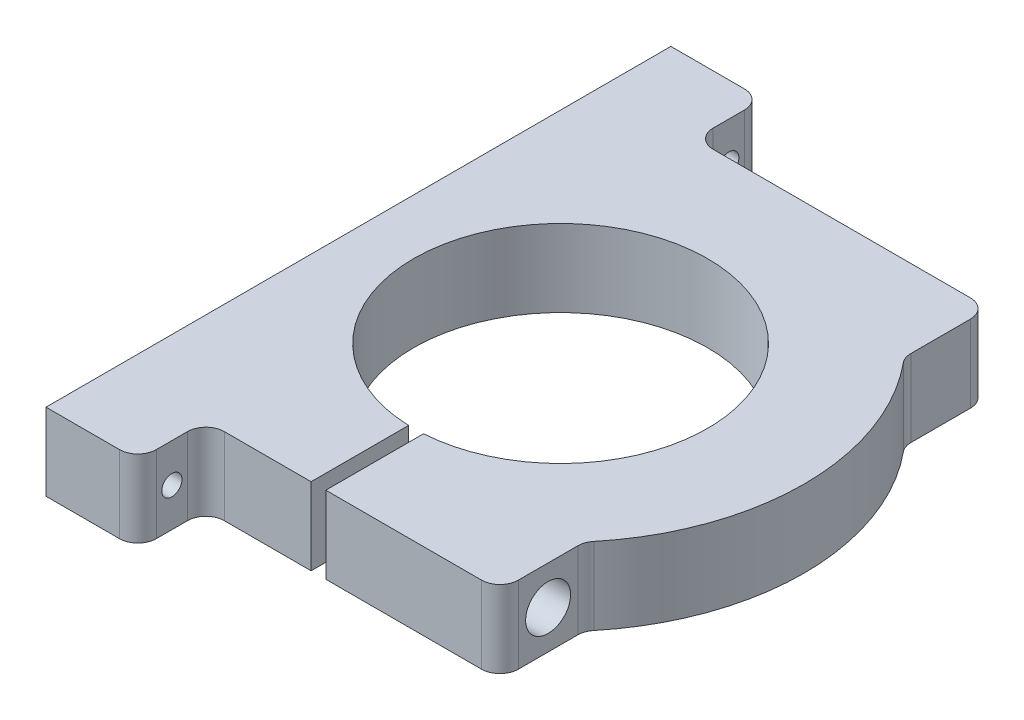
SolidWorks part; units mm, degrees
ref_plane "Piano frontale" through (0, 0, 0) normal (0, 0, 1) x (1, 0, 0)
ref_plane "Piano superiore" through (0, 0, 0) normal (0, 1, 0) x (1, 0, 0)
ref_plane "Piano destro" through (0, 0, 0) normal (1, 0, 0) x (0, 0, -1)
sketch "Sketch1" plane through (0, 0, -219.72) normal (0, -1, 0) x (1, 0, 0)
  line L2 (7.3254, -97.2179) -> (7.3254, -57.6696) construction
  line L3 (-32.6746, -97.2179) -> (7.3254, -97.2179) construction
  line L4 (17.3254, -30.7179) -> (-30.0496, -30.7179)
  line L5 (-62.6746, -30.7179) -> (-62.6746, -12.2179)
  line L6 (-62.6746, -12.2179) -> (-87.6746, -12.2179)
  line L7 (-34.0496, -30.7179) -> (-62.6746, -30.7179)
  line L8 (-40.0496, -30.7179) -> (-40.0496, -68.1385) construction
  line L9 (-24.0496, -68.4844) -> (-24.0496, -30.7179) construction
  line L10 (-87.6746, -182.2179) -> (-62.6746, -182.2179)
  line L11 (-62.6746, -182.2179) -> (-62.6746, -163.7179)
  line L12 (-87.6746, -22.2179) -> (-87.6746, -172.2179) construction
  line L13 (-62.6746, -163.7179) -> (17.3254, -163.7179)
  line L14 (17.3254, -163.7179) -> (17.3254, -140.6812)
  line L15 (17.3254, -53.7545) -> (17.3254, -30.7179)
  line L16 (-72.6746, -153.7179) -> (7.3254, -153.7179) construction
  line L17 (-34.0496, -40.7179) -> (-72.6746, -40.7179) construction
  line L18 (-34.0496, -57.2415) -> (-34.0496, -40.7179) construction
  line L19 (-30.0496, -40.7179) -> (-30.0496, -57.3041) construction
  line L21 (17.3254, -30.7179) -> (-40.0496, -30.7179) construction
  line L23 (-24.0496, -30.7179) -> (-62.6746, -30.7179) construction
  line L24 (-30.0496, -30.7179) -> (-30.0496, -57.3041)
  line L25 (-34.0496, -57.2415) -> (-34.0496, -30.7179)
  line L29 (-87.6746, -12.2179) -> (-87.6746, -182.2179)
  line L36 (-62.6746, -12.2179) -> (-97.6746, -12.2179) construction
  line L37 (-97.6746, -12.2179) -> (-97.6746, -182.2179) construction
  line L38 (-97.6746, -182.2179) -> (-62.6746, -182.2179) construction
  line L39 (-62.6746, -182.2179) -> (-62.6746, -163.7179) construction
  line L40 (-62.6746, -30.7179) -> (-62.6746, -12.2179) construction
  line L41 (-72.6746, -172.2179) -> (-72.6746, -153.7179) construction
  line L42 (-87.6746, -172.2179) -> (-72.6746, -172.2179) construction
  line L43 (-72.6746, -22.2179) -> (-87.6746, -22.2179) construction
  line L44 (-72.6746, -40.7179) -> (-72.6746, -22.2179) construction
  line L45 (7.3254, -40.7179) -> (-30.0496, -40.7179) construction
  line L46 (7.3254, -57.6696) -> (7.3254, -40.7179) construction
  line L47 (7.3254, -153.7179) -> (7.3254, -136.7661) construction
  arc A2 (7.3254, -136.7661) -> (7.3254, -57.6696) centre (-32.6746, -97.2179) ccw construction
  arc A3 (17.3254, -140.6812) -> (17.3254, -53.7545) centre (-32.6746, -97.2179) ccw
  arc A4 (-34.0496, -57.2415) -> (-30.0496, -57.3041) centre (-32.6746, -97.2179) ccw
  arc A5 (-24.0496, -68.4844) -> (-40.0496, -68.1385) centre (-32.6746, -97.2179) ccw construction
  dimension "D2" = 4
  dimension "D1" = 10
extrude "Boss-Extrude2" add sketch "Sketch1" along normal blind 21
fillet "Fillet2" radius 5 8 edges at (-62.6746, -10.5, -231.9379) (-62.6746, -10.5, -250.4379) (17.3254, -10.5, -250.4379) (-62.6746, -10.5, -401.9379) (-62.6746, -10.5, -383.4379) (17.3254, -10.5, -383.4379) (17.3254, -10.5, -360.4012) (17.3254, -10.5, -273.4745)
hole_wizard "M5 Clearance Hole1" positions "Sketch4" profile "Sketch5" hole size "M5" standard "ISO" end condition through all
sketch "Sketch4" plane through (17.3254, 0, 0) normal (1, 0, 0) x (0, 0, -1)
  line L0 (241.1879, 0) -> (241.1879, -21) construction
  line L1 (245.4379, 0) -> (236.9379, 0) construction
  line L2 (245.4379, -21) -> (236.9379, -21) construction
  line L4 (392.6879, 0) -> (392.6879, -21) construction
  line L5 (396.9379, 0) -> (388.4379, 0) construction
  line L6 (396.9379, -21) -> (388.4379, -21) construction
  point P23 (241.1879, -10.5)
  point P25 (392.6879, -10.5)
sketch "Sketch5" plane through (17.3254, -10.5, -392.6879) normal (0, 1, 0) x (0, 0, -1)
  line L0 (0, 0) -> (0, 105)
  line L1 (0, 105) -> (2.75, 105)
  line L2 (2.75, 105) -> (2.75, 0)
  line L5 (2.75, 0) -> (0, 0)
  line L11 (0, -6.35) -> (0, 107.95) construction
  dimension "Thru Hole Dia." = 5.5
  dimension "Thru Hole Depth" = 105
hole_wizard "CBORE for M5 Hex Head Bolt1" positions "Sketch6" profile "Sketch7" counterbore size "M5" standard "ISO" end condition up to next
sketch "Sketch6" plane through (17.3254, 0, 0) normal (1, 0, 0) x (0, 0, -1)
  line L0 (263.5408, 0) -> (263.5408, -21) construction
  line L1 (271.6437, 0) -> (255.4379, 0) construction
  line L2 (271.6437, -21) -> (255.4379, -21) construction
  point P0 (263.5408, -10.5)
sketch "Sketch7" plane through (17.3254, -10.5, -263.5408) normal (0, 1, 0) x (0, 0, -1)
  line L0 (0, 0) -> (0, 47.375)
  line L1 (0, 47.375) -> (2.75, 47.375)
  line L3 (2.75, 47.375) -> (2.75, 23.5)
  line L4 (2.75, 23.5) -> (6.119, 23.5)
  line L5 (6.119, 23.5) -> (6.119, 0)
  line L7 (6.119, 0) -> (0, 0)
  line L11 (0, -6.35) -> (0, 107.95) construction
  dimension "Thru Hole Dia." = 5.5
  dimension "Thru Hole Depth" = 47.375
  dimension "C'Bore Dia." = 12.238
  dimension "C'Bore Depth" = 23.5
hole_wizard "Tap Drill for M5 Tap1" positions "Sketch8" profile "Sketch9" hole size "M5" standard "ISO" end condition up to next
sketch "Sketch8" plane through (-34.0496, 0, 0) normal (1, 0, 0) x (0, 0, -1)
  point P0 (263.5408, -10.5)
sketch "Sketch9" plane through (-34.0496, -10.5, -263.5408) normal (0, 1, 0) x (0, 0, -1)
  line L0 (0, 0) -> (0, 53.625)
  line L1 (0, 53.625) -> (2.1, 53.625)
  line L2 (2.1, 53.625) -> (2.1, 0)
  line L5 (2.1, 0) -> (0, 0)
  line L11 (0, -6.35) -> (0, 107.95) construction
  dimension "Thru Hole Dia." = 4.2
  dimension "Thru Hole Depth" = 53.625
hole_wizard "M8 Clearance Hole1" positions "Sketch10" profile "Sketch11" hole size "M8" standard "ISO"
sketch "Sketch10" plane through (0, 0, 0) normal (0, 1, 0) x (1, 0, 0)
  point P0 (5.6543, 370.335)
  point P2 (12.5599, 287.0353)
  point P4 (-60.405, 369.1208)
  point P6 (-69.265, 276.742)
sketch "Sketch11" plane through (5.6543, 0, -370.335) normal (1, 0, 0) x (0, 0, 1)
  line L0 (0, 0) -> (0, 30)
  line L1 (0, 30) -> (4.5, 30)
  line L2 (4.5, 30) -> (4.5, 0)
  line L5 (4.5, 0) -> (0, 0)
  line L11 (0, -6.35) -> (0, 107.95) construction
  dimension "Thru Hole Dia." = 9
  dimension "Thru Hole Depth" = 30
